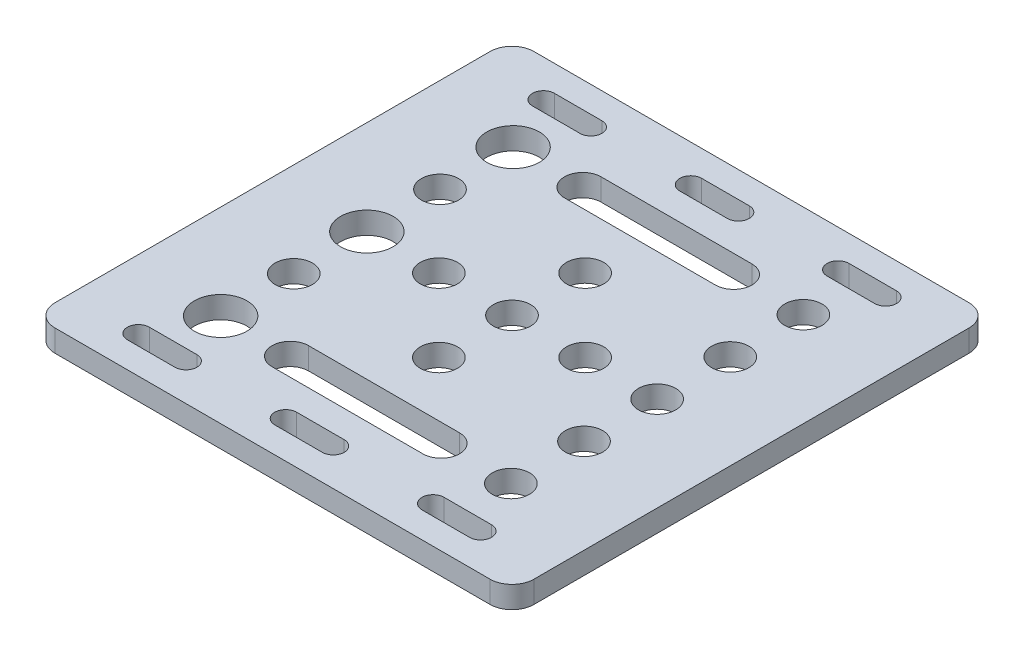
SolidWorks part; units mm, degrees
material "6061-T6 (SS)"
ref_plane "Front Plane" through (0, 0, 0) normal (0, 0, 1) x (1, 0, 0)
ref_plane "Top Plane" through (0, 0, 0) normal (0, 1, 0) x (1, 0, 0)
ref_plane "Right Plane" through (0, 0, 0) normal (1, 0, 0) x (0, 0, -1)
sketch "Sketch1" plane through (0, 0, 0) normal (0, 1, 0) x (1, 0, 0)
  line L0 (0, 0) -> (32.75, 0) construction
  line L1 (29.75, -32.75) -> (-29.75, -32.75)
  line L2 (32.75, -29.75) -> (32.75, 29.75)
  line L3 (29.75, 32.75) -> (-29.75, 32.75)
  line L4 (-32.75, -29.75) -> (-32.75, 29.75)
  line L5 (0, 32.75) -> (0, 0) construction
  line L6 (-29.75, 44) -> (92.25, 44) construction
  line L9 (10.32, 20) -> (-10.32, 20) construction
  line L10 (10.32, 17.5) -> (-10.32, 17.5)
  line L11 (10.32, 22.5) -> (-10.32, 22.5)
  line L12 (3.25, 27.7) -> (-3.25, 27.7) construction
  line L13 (3.25, 26.2) -> (-3.25, 26.2)
  line L14 (3.25, 29.2) -> (-3.25, 29.2)
  line L15 (-16.9, 27.7) -> (-23.4, 27.7) construction
  line L16 (-16.9, 26.2) -> (-23.4, 26.2)
  line L17 (-16.9, 29.2) -> (-23.4, 29.2)
  line L18 (16.9, 27.7) -> (23.4, 27.7) construction
  line L19 (16.9, 26.2) -> (23.4, 26.2)
  line L20 (16.9, 29.2) -> (23.4, 29.2)
  line L21 (10.32, -20) -> (-10.32, -20) construction
  line L22 (10.32, -17.5) -> (-10.32, -17.5)
  line L23 (10.32, -22.5) -> (-10.32, -22.5)
  line L24 (-16.9, -27.7) -> (-23.4, -27.7) construction
  line L25 (-16.9, -26.2) -> (-23.4, -26.2)
  line L26 (-16.9, -29.2) -> (-23.4, -29.2)
  line L27 (3.25, -27.7) -> (-3.25, -27.7) construction
  line L28 (3.25, -26.2) -> (-3.25, -26.2)
  line L29 (3.25, -29.2) -> (-3.25, -29.2)
  line L30 (16.9, -27.7) -> (23.4, -27.7) construction
  line L31 (16.9, -26.2) -> (23.4, -26.2)
  line L32 (16.9, -29.2) -> (23.4, -29.2)
  arc A0 (-29.75, -32.75) -> (-32.75, -29.75) centre (-29.75, -29.75) cw
  arc A1 (29.75, -32.75) -> (32.75, -29.75) centre (29.75, -29.75) ccw
  arc A2 (32.75, 29.75) -> (29.75, 32.75) centre (29.75, 29.75) ccw
  arc A3 (-29.75, 32.75) -> (-32.75, 29.75) centre (-29.75, 29.75) ccw
  circle A5 centre (0, 10) radius 2.55
  circle A6 centre (0, 0) radius 2.55
  circle A7 centre (10, 0) radius 2.55
  circle A8 centre (-10, 0) radius 2.55
  circle A9 centre (-19.85, 20) radius 3.6
  circle A10 centre (-19.85, 0) radius 3.6
  circle A11 centre (-19.85, -20) radius 3.6
  circle A16 centre (-19.85, 10) radius 2.55
  circle A24 centre (19.85, 20) radius 2.55
  circle A25 centre (19.85, 0) radius 2.55
  circle A27 centre (19.85, -20) radius 2.55
  circle A30 centre (0, -10) radius 2.55
  circle A46 centre (19.85, 10) radius 2.55
  circle A54 centre (19.85, -10) radius 2.55
  circle A63 centre (-19.85, -10) radius 2.55
  arc A67 (10.32, 17.5) -> (10.32, 22.5) centre (10.32, 20) ccw
  arc A68 (-10.32, 22.5) -> (-10.32, 17.5) centre (-10.32, 20) ccw
  arc A69 (3.25, 26.2) -> (3.25, 29.2) centre (3.25, 27.7) ccw
  arc A70 (-3.25, 29.2) -> (-3.25, 26.2) centre (-3.25, 27.7) ccw
  arc A71 (-16.9, 26.2) -> (-16.9, 29.2) centre (-16.9, 27.7) ccw
  arc A72 (-23.4, 29.2) -> (-23.4, 26.2) centre (-23.4, 27.7) ccw
  arc A73 (16.9, 26.2) -> (16.9, 29.2) centre (16.9, 27.7) cw
  arc A74 (23.4, 29.2) -> (23.4, 26.2) centre (23.4, 27.7) cw
  arc A75 (10.32, -17.5) -> (10.32, -22.5) centre (10.32, -20) cw
  arc A76 (-10.32, -22.5) -> (-10.32, -17.5) centre (-10.32, -20) cw
  arc A77 (-16.9, -26.2) -> (-16.9, -29.2) centre (-16.9, -27.7) cw
  arc A78 (-23.4, -29.2) -> (-23.4, -26.2) centre (-23.4, -27.7) cw
  arc A79 (3.25, -26.2) -> (3.25, -29.2) centre (3.25, -27.7) cw
  arc A80 (-3.25, -29.2) -> (-3.25, -26.2) centre (-3.25, -27.7) cw
  arc A81 (16.9, -26.2) -> (16.9, -29.2) centre (16.9, -27.7) ccw
  arc A82 (23.4, -29.2) -> (23.4, -26.2) centre (23.4, -27.7) ccw
  point P0 (0, 0)
  point P149 (0, 20)
  point P156 (0, 27.7)
  point P162 (-20.15, 27.7)
  point P170 (20.15, 27.7)
  point P177 (0, -20)
  point P184 (-20.15, -27.7)
  point P191 (0, -27.7)
  point P198 (20.15, -27.7)
  dimension "D2" = 3
  dimension "D3" = 5.1
  dimension "D5" = 7.2
  dimension "D10" = 10
  dimension "D1" = 65.5
  dimension "D4" = 10
  dimension "D6" = 40
  dimension "D8" = 12.9
  dimension "D9" = 65.5
  dimension "D14" = 10
  dimension "D16" = 39.7
  dimension "D25" = 5
  dimension "D26" = 20.64
  dimension "D27" = 6.5
  dimension "D28" = 3
  dimension "D29" = 20.15
  dimension "D30" = 40
  dimension "D31" = 55.4
extrude "Boss-Extrude1" add sketch "Sketch1" along normal blind 3
